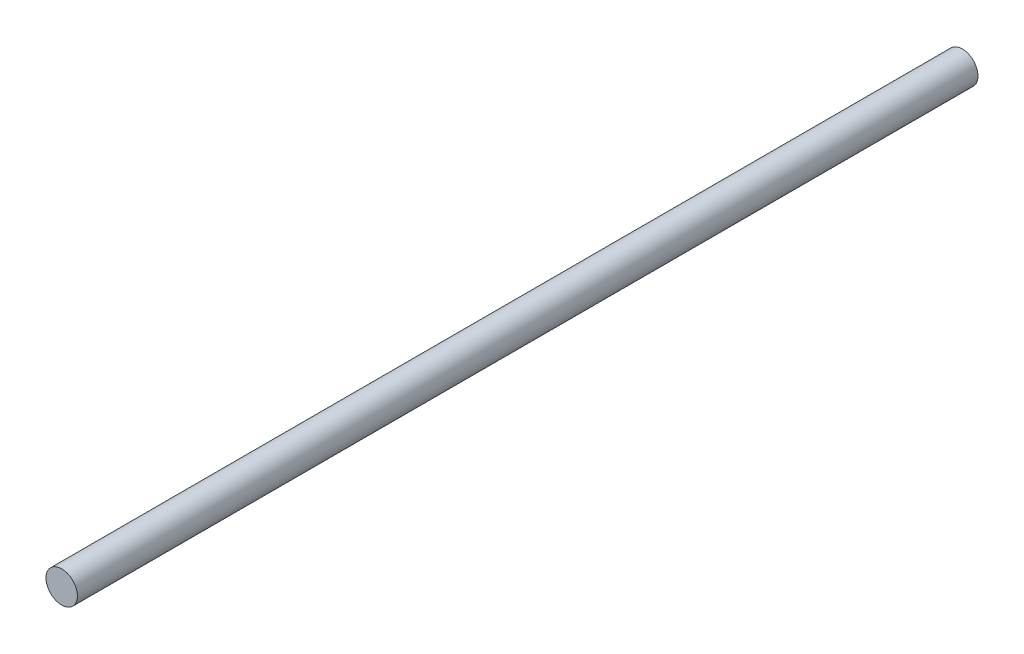
SolidWorks part; units mm, degrees
ref_plane "Plan de face" through (0, 0, 0) normal (0, 0, 1) x (1, 0, 0)
ref_plane "Plan de dessus" through (0, 0, 0) normal (0, 1, 0) x (1, 0, 0)
ref_plane "Plan de droite" through (0, 0, 0) normal (1, 0, 0) x (0, 0, -1)
sketch "Esquisse1" plane through (0, 0, 0) normal (0, 0, 1) x (1, 0, 0)
  circle A0 centre (0, 0) radius 3
  dimension "D1" = 6
extrude "Boss.-Extru.1" add sketch "Esquisse1" along normal blind 172
